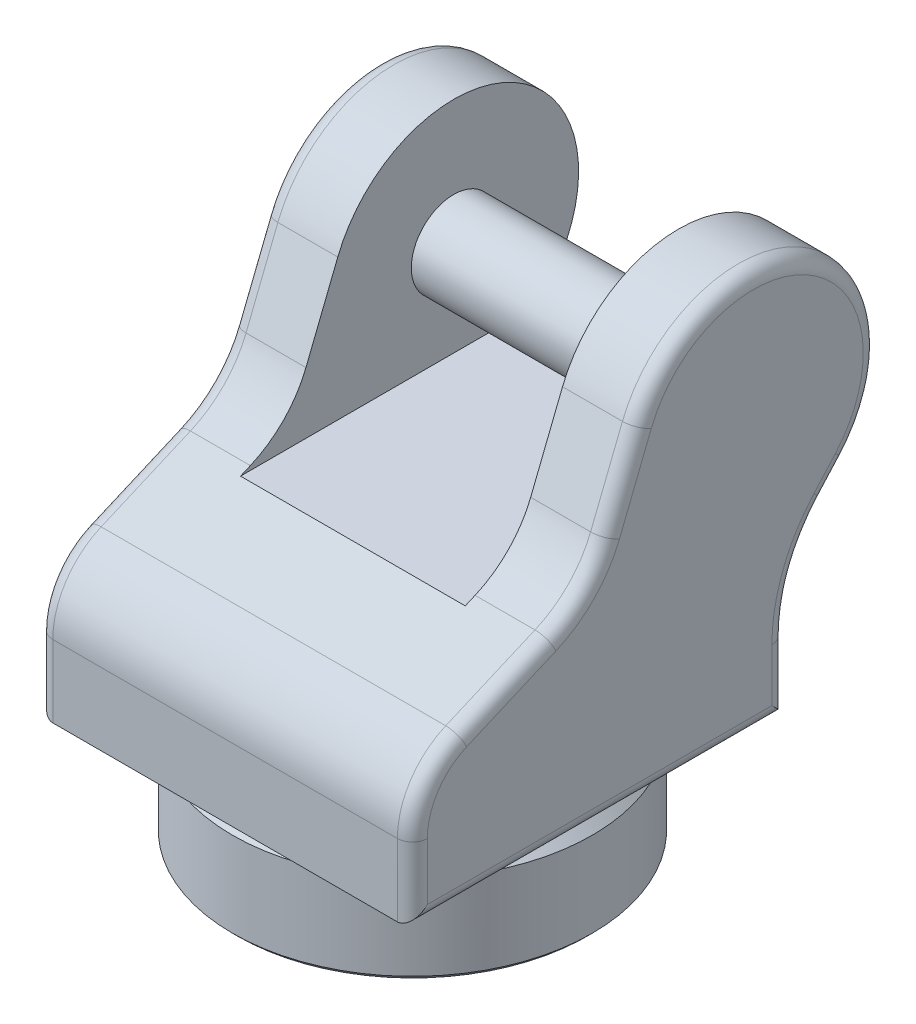
SolidWorks part; units mm, degrees
material "Balsa"
ref_plane "Front Plane" through (0, 0, 0) normal (0, 0, 1) x (1, 0, 0)
ref_plane "Top Plane" through (0, 0, 0) normal (0, 1, 0) x (1, 0, 0)
ref_plane "Right Plane" through (0, 0, 0) normal (1, 0, 0) x (0, 0, -1)
sketch "Sketch2" plane through (0, 0, 0) normal (0, 0, 1) x (1, 0, 0)
  line L0 (-160, 0) -> (-160, 20)
  line L2 (0, 0) -> (-180, 0) construction
  line L10 (0, 0) -> (0, 100) construction
  line L11 (0, 100) -> (-180, 100)
  line L12 (-180, 0) -> (-180, 100)
  line L13 (-160, 20) -> (-150, 20)
  line L14 (-150, 20) -> (-150, 80)
  line L15 (-150, 80) -> (0, 80)
  line L16 (-180, 0) -> (-160, 0)
  line L17 (0, 100) -> (0, 80)
  dimension "D1" = 180
  dimension "D2" = 100
  dimension "D3" = 20
  dimension "D4" = 60
  dimension "D5" = 160
  dimension "D6" = 150
revolve "Revolve1" add sketch "Sketch2" angle 360 about L17
chamfer "Chamfer1" distance 10 angle 45 1 edges at (0, 100, 180)
chamfer "Chamfer2" distance 5 angle 45 2 edges at (0, 80, 150) (0, 0, 160)
chamfer "Chamfer3" distance 5 angle 45 1 edges at (0, 0, 180)
sketch "Sketch4" plane through (0, 100, 0) normal (0, 1, 0) x (1, 0, 0)
  circle A0 centre (0, 0) radius 160
  dimension "D1" = 320
extrude "Boss-Extrude1" add sketch "Sketch4" along normal blind 5
sketch "Sketch5" plane through (0, 0, 0) normal (1, 0, 0) x (0, 0, -1)
  line L0 (187.4372, 105) -> (-187.5628, 105)
  line L1 (153.8991, 380) -> (-0.0628, 105) construction
  line L2 (-187.5628, 105) -> (-187.5628, 177.3072)
  line L3 (-187.5628, 230) -> (187.4372, 230) construction
  line L4 (187.4372, 172.703) -> (187.4372, 105)
  line L5 (247.0665, 296.6644) -> (225.6362, 272.7057)
  line L6 (37.7919, 426.3046) -> (5.9239, 346.397)
  line L7 (0, 0) -> (-0.0628, 105) construction
  line L8 (-49.7518, 289.2294) -> (-139.1519, 250.8064)
  arc A0 (247.0665, 296.6644) -> (37.7919, 426.3046) centre (153.8991, 380) ccw
  arc A2 (187.4372, 172.703) -> (225.6362, 272.7057) centre (337.4372, 172.703) cw
  arc A4 (5.9239, 346.397) -> (-49.7518, 289.2294) centre (-90.9213, 385.0198) cw
  arc A5 (-187.5628, 177.3072) -> (-139.1519, 250.8064) centre (-107.5628, 177.3072) cw
  point P3 (-0.0628, 105)
  dimension "D3" = 250
  dimension "D5" = 135
  dimension "D8" = 150
  dimension "D9" = 80
  dimension "D1" = 375
  dimension "D2" = 125
  dimension "D4" = 150
  dimension "D6" = 150
  dimension "D7" = 89.4416
  dimension "D11" = 105
extrude "Boss-Extrude2" add sketch "Sketch5" along normal mid plane 375
fillet "Fillet1" radius 15 20 edges at (-187.5, 105, 0.0628) (-187.5, 138.8515, -187.4372) (-187.5, 226.228, -197.312) (-187.5, 284.6851, -236.3514) (-187.5, 486.2629, -219.7261) (-187.5, 141.1536, 187.5628) (187.5, 486.2629, -219.7261) (187.5, 284.6851, -236.3514) (187.5, 226.228, -197.312) (187.5, 138.8515, -187.4372) (187.5, 105, 0.0628) (187.5, 141.1536, 187.5628) (-187.5, 386.3508, -21.8579) (-187.5, 312.2759, 16.2283) (-187.5, 270.0179, 94.4518) (-187.5, 221.3122, 174.3727) (187.5, 221.3122, 174.3727) (187.5, 270.0179, 94.4518) (187.5, 312.2759, 16.2283) (187.5, 386.3508, -21.8579)
sketch "Sketch6" plane through (0, 0, 0) normal (0, 0, 1) x (1, 0, 0)
  line L0 (172.5, 505) -> (-172.5, 505) construction
  line L1 (-112.5, 505) -> (112.5, 505)
  line L2 (-112.5, 505) -> (-112.5, 285)
  line L3 (-112.5, 285) -> (112.5, 285)
  line L4 (112.5, 505) -> (112.5, 285)
  line L5 (-187.5, 490) -> (-187.5, 306.6647) construction
  line L6 (187.5, 306.6647) -> (187.5, 490) construction
  dimension "D1" = 75
  dimension "D2" = 75
  dimension "D3" = 220
extrude "Cut-Extrude1" cut sketch "Sketch6" against normal through all both and the other way through all
sketch "Sketch7" plane through (112.5, 0, 0) normal (-1, 0, 0) x (0, 0, 1)
  circle A1 centre (-153.8991, 380) radius 42.5
  arc A3 (-37.7919, 426.3046) -> (-247.0665, 296.6644) centre (-153.8991, 380) ccw construction
  arc A4 (-37.7919, 426.3046) -> (-247.0665, 296.6644) centre (-153.8991, 380) ccw construction
  dimension "D1" = 85
extrude "Boss-Extrude3" add sketch "Sketch7" along normal up to surface (225 mm away) up to face at (-112.5, 341.3061, -83.5089)
sketch "Sketch8" plane through (0, 0, 0) normal (0, 0, 1) x (1, 0, 0)
  line L0 (-150, 75) -> (-150, 20) construction
  line L1 (-150, 60) -> (-140, 60)
  line L2 (-150, 60) -> (-150, 47.5)
  line L3 (-150, 47.5) -> (-140, 47.5)
  line L4 (-140, 60) -> (-140, 47.5)
  line L5 (-145, 80) -> (145, 80) construction
  line L6 (0, 0) -> (0, 43.929) construction
  dimension "D1" = 20
  dimension "D2" = 12.5
  dimension "D3" = 10
revolve "Revolve2" add sketch "Sketch8" angle 360 about L6
